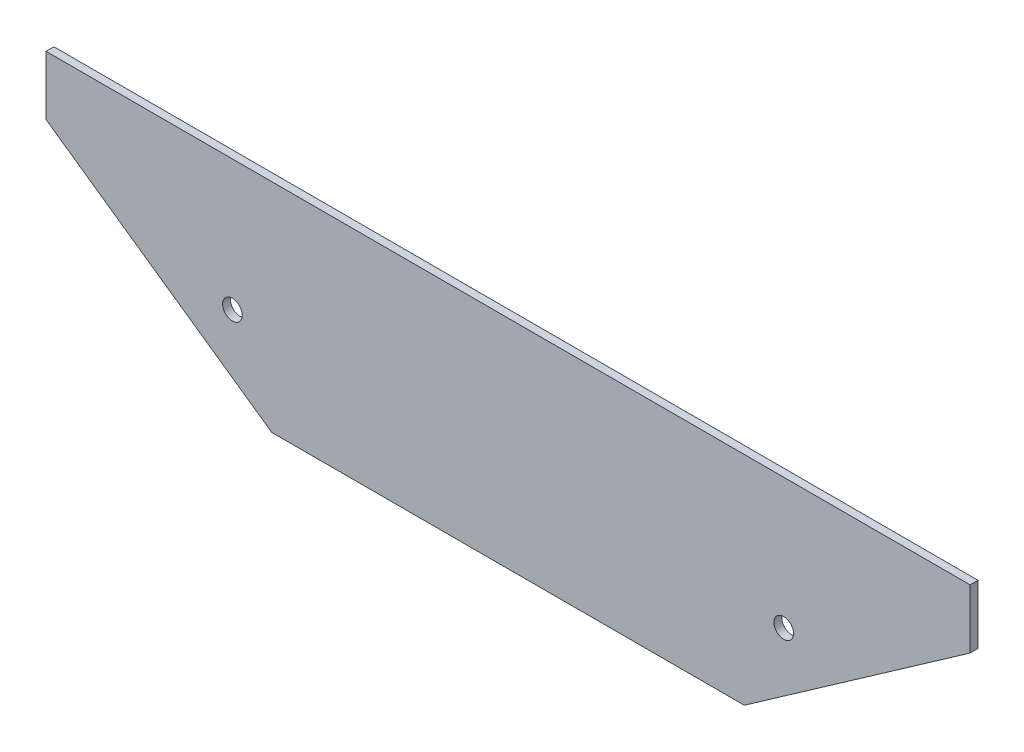
SolidWorks part; units mm, degrees
material "1060 Alloy"
ref_plane "Front Plane" through (0, 0, 0) normal (0, 0, 1) x (1, 0, 0)
ref_plane "Top Plane" through (0, 0, 0) normal (0, 1, 0) x (1, 0, 0)
ref_plane "Right Plane" through (0, 0, 0) normal (1, 0, 0) x (0, 0, -1)
sketch "Sketch1" plane through (0, 0, 92) normal (0, 0, 1) x (1, 0, 0)
  line L8 (-19.1645, -18.5514) -> (-23.8699, -23.5974)
  line L9 (-27.2799, -27.2541) -> (-0.8896, 1.046) construction
  line L10 (-23.8699, -23.5974) -> (-16.9704, -23.5974)
  line L11 (227.6594, -63.7477) -> (402.6594, -63.7477)
  line L12 (402.6594, -63.7477) -> (460, -23.5974)
  line L13 (510, -1) -> (510, -23.5974) construction
  line L14 (243.065, -41.7477) -> (243.065, -8.5974) construction
  line L15 (26.1301, -23.5974) -> (460, -23.5974)
  line L16 (-1.865, 0) -> (-19.1645, -18.5514)
  line L17 (-16.9704, -23.5974) -> (26.1301, -23.5974)
  line L18 (26.1301, -23.5974) -> (83.4707, -63.7477)
  line L19 (83.4707, -63.7477) -> (227.6594, -63.7477)
  line L20 (227.6594, -63.7477) -> (285, -23.5974)
  line L21 (285, -23.5974) -> (507, -23.5974)
  line L22 (507, -23.5974) -> (507, 0)
  line L23 (507, 0) -> (-1.865, 0)
  line L24 (-1.865, 0) -> (-19.1645, -18.5514)
  line L25 (-16.9704, -23.5974) -> (26.1301, -23.5974)
  line L26 (26.1301, -23.5974) -> (83.4707, -63.7477)
  line L27 (83.4707, -63.7477) -> (227.6594, -63.7477)
  line L28 (227.6594, -63.7477) -> (285, -23.5974)
  line L29 (285, -23.5974) -> (507, -23.5974)
  line L30 (507, -23.5974) -> (507, 0)
  line L31 (507, 0) -> (-1.865, 0)
  line L32 (26.1301, -23.5974) -> (26.1301, -8.5974)
  line L33 (26.1301, -8.5974) -> (460, -8.5974)
  line L34 (460, -23.5974) -> (460, -8.5974)
  line L36 (83.4707, -41.7477) -> (402.6594, -41.7477) construction
  line L37 (83.4707, -63.7477) -> (83.4707, -41.7477) construction
  line L38 (402.6594, -63.7477) -> (402.6594, -41.7477) construction
  arc A2 (-19.1645, -18.5514) -> (-16.9704, -23.5974) centre (-16.9704, -20.5974) ccw
  arc A3 (-19.1645, -18.5514) -> (-16.9704, -23.5974) centre (-16.9704, -20.5974) ccw
  circle A5 centre (313.065, -41.7477) radius 2.5
  circle A6 centre (225.565, -41.7477) radius 2.5
  circle A7 centre (225.565, -41.7477) radius 2.5
  circle A9 centre (173.065, -41.7477) radius 2.5
  circle M15 centre (225.565, -41.7477) radius 2.5
  circle M16 centre (85.565, -41.7477) radius 2.5
  line M20 (26.1301, -23.5974) -> (83.4707, -63.7477)
  line M21 (83.4707, -63.7477) -> (227.6594, -63.7477)
  line M22 (227.6594, -63.7477) -> (285, -23.5974)
  line M23 (285, -23.5974) -> (507, -23.5974)
  dimension "D6" = 0
  dimension "D7" = 5
  dimension "D8" = 70
  dimension "D2" = 145
  dimension "D3" = 50
  dimension "D4" = 15
  dimension "D5" = 0
  dimension "D1" = 0
extrude "Boss-Extrude1" add sketch "Sketch1" along normal blind 2 contours L34 L33 L32 L15 M23 | L11 L12 M23 M22 | L15 M20 M21 M22 M16 M15 | M16 | M15
sketch "Sketch2" plane through (0, 0, 92) normal (0, 0, -1) x (-1, 0, 0)
  line L1 (-125.7244, -23.5974) -> (-360.4057, -23.5974)
  line L2 (-125.7244, -23.5974) -> (-125.7244, -8.5974)
  line L3 (-125.7244, -8.5974) -> (-360.4057, -8.5974)
  line L4 (-360.4057, -23.5974) -> (-360.4057, -8.5974)
  line L6 (-243.065, -63.7477) -> (-243.065, -8.5974) construction
  line L7 (-183.065, -63.7477) -> (-104.3022, -8.5974)
  line L8 (-303.065, -63.7477) -> (-381.8279, -8.5974)
  line L12 (-26.1301, -23.5974) -> (-26.1301, -8.5974)
  line L13 (-26.1301, -8.5974) -> (-460, -8.5974)
  line L14 (-460, -8.5974) -> (-460, -23.5974)
  line L15 (-460, -23.5974) -> (-402.6594, -63.7477)
  line L16 (-402.6594, -63.7477) -> (-83.4707, -63.7477)
  line L17 (-83.4707, -63.7477) -> (-26.1301, -23.5974)
  line L18 (-26.1301, -23.5974) -> (-26.1301, -8.5974)
  line L19 (-26.1301, -8.5974) -> (-460, -8.5974)
  line L20 (-460, -8.5974) -> (-460, -23.5974)
  line L21 (-460, -23.5974) -> (-402.6594, -63.7477)
  line L22 (-402.6594, -63.7477) -> (-83.4707, -63.7477)
  line L23 (-83.4707, -63.7477) -> (-26.1301, -23.5974)
  line M10 (-26.1301, -23.5974) -> (-26.1301, -8.5974)
  line M11 (-26.1301, -8.5974) -> (-460, -8.5974)
  line M12 (-460, -8.5974) -> (-460, -23.5974)
  line M13 (-460, -23.5974) -> (-402.6594, -63.7477)
  line M14 (-402.6594, -63.7477) -> (-83.4707, -63.7477)
  line M15 (-83.4707, -63.7477) -> (-26.1301, -23.5974)
  dimension "D2" = 60
  dimension "D1" = 0
extrude "Cut-Extrude1" cut sketch "Sketch2" against normal blind 10 contours L8 L4 M11 | L8 M14 M11 M12 M13 | L2 L7 M11 | L7 M14 M15 M10 M11
